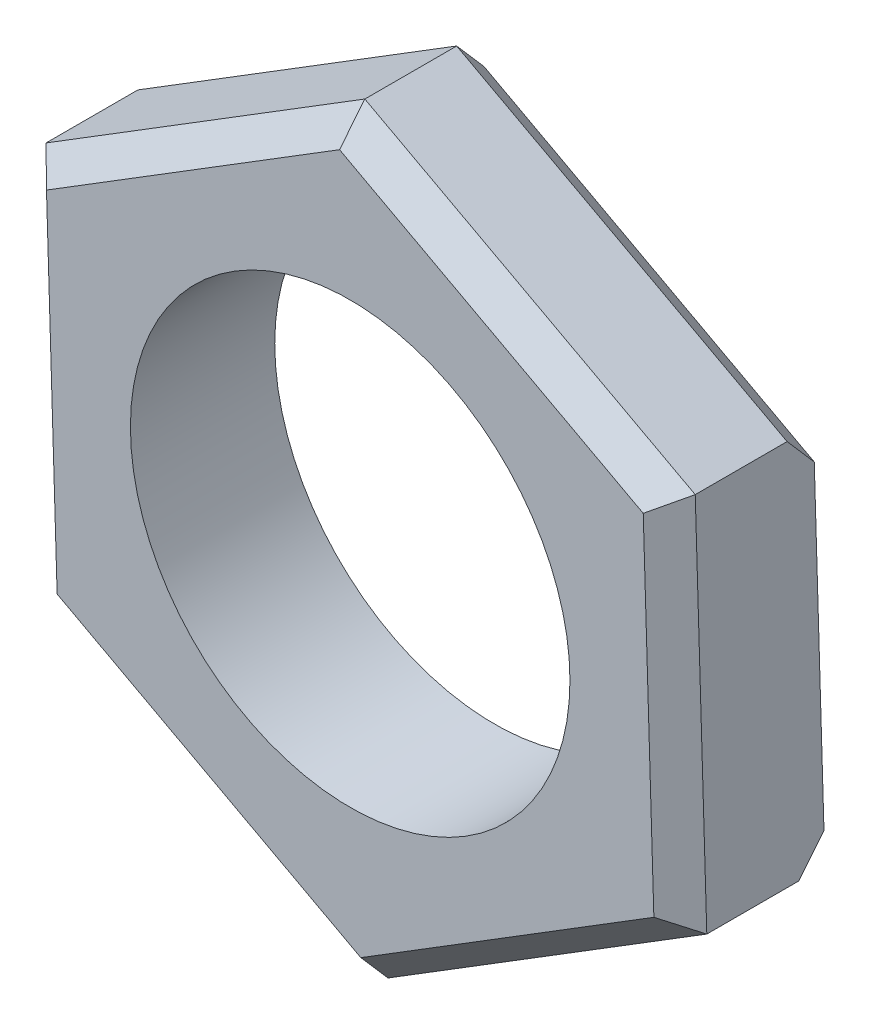
SolidWorks part; units mm, degrees
ref_plane "前视基准面" through (0, 0, 0) normal (0, 0, 1) x (1, 0, 0)
ref_plane "上视基准面" through (0, 0, 0) normal (0, 1, 0) x (1, 0, 0)
ref_plane "右视基准面" through (0, 0, 0) normal (1, 0, 0) x (0, 0, -1)
sketch "草图1" plane through (0, 0, 0) normal (0, 0, 1) x (1, 0, 0)
  line L1 (5.0359, -2.7037) -> (4.8594, 3.0094)
  line L2 (4.8594, 3.0094) -> (-0.1765, 5.713)
  line L3 (-0.1765, 5.713) -> (-5.0359, 2.7037)
  line L4 (-5.0359, 2.7037) -> (-4.8594, -3.0094)
  line L5 (-4.8594, -3.0094) -> (0.1765, -5.713)
  line L6 (0.1765, -5.713) -> (5.0359, -2.7037)
  circle A0 centre (0, 0) radius 4.95 construction
  circle A1 centre (0, 0) radius 3.35
  dimension "D2" = 6.7
  dimension "D1" = 9.9
extrude "凸台-拉伸1" add sketch "草图1" along normal blind 2.2
cosmetic thread "装饰螺纹线1" parameters "D2"=20.1
chamfer "倒角1" distance 0.4 angle 45 11 edges at (2.3415, 4.3612, 0) (-2.6062, 4.2084, 0) (-4.9476, -0.1528, 0) (-2.3415, -4.3612, 0) (2.6062, -4.2084, 0) (4.9476, 0.1528, 2.2) (2.6062, -4.2084, 2.2) (-2.3415, -4.3612, 2.2) (-4.9476, -0.1528, 2.2) (-2.6062, 4.2084, 2.2) (2.3415, 4.3612, 2.2)
